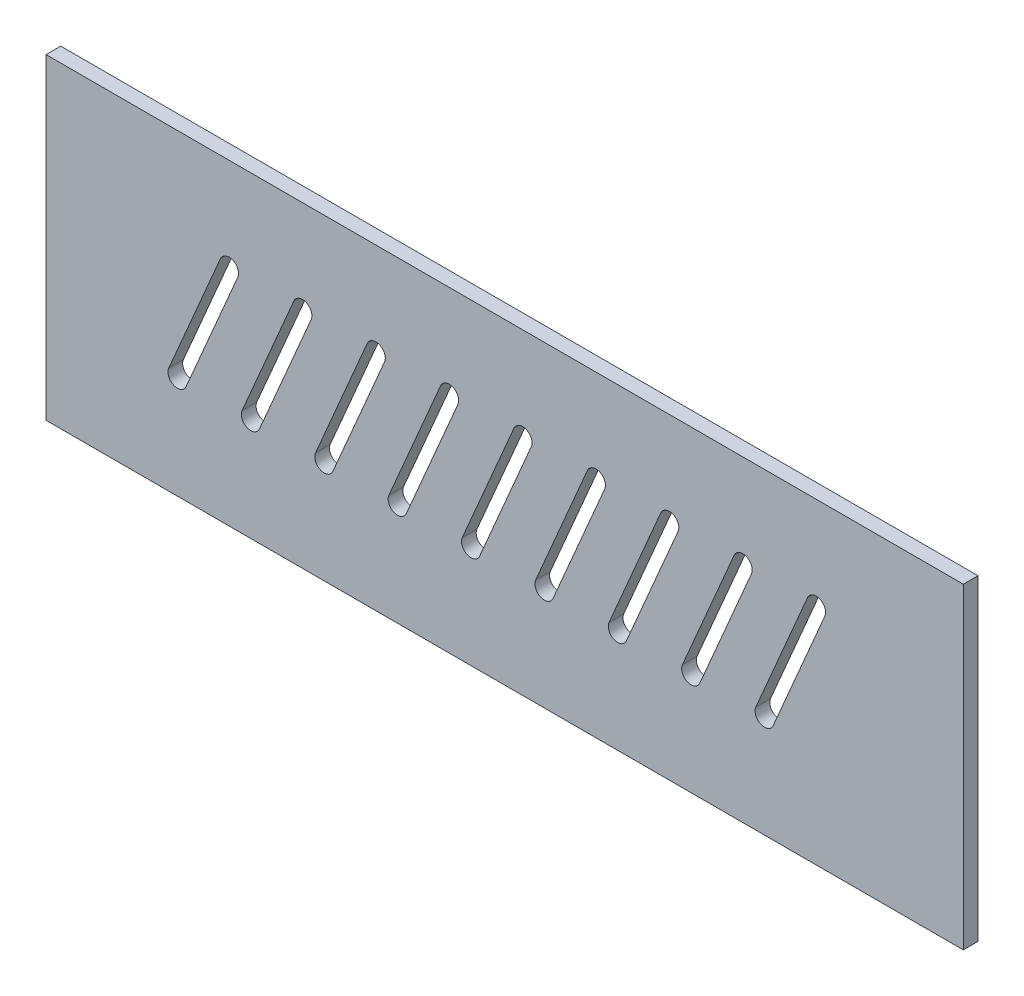
SolidWorks part; units mm, degrees
ref_plane "Front Plane" through (0, 0, 0) normal (0, 0, 1) x (1, 0, 0)
ref_plane "Top Plane" through (0, 0, 0) normal (0, 1, 0) x (1, 0, 0)
ref_plane "Right Plane" through (0, 0, 0) normal (1, 0, 0) x (0, 0, -1)
sketch "Sketch1" plane through (0, 0, 0) normal (0, 0, 1) x (1, 0, 0)
  line L1 (-62.5, 32.5) -> (62.5, 32.5)
  line L2 (-62.5, 32.5) -> (-62.5, -32.5)
  line L3 (-62.5, -32.5) -> (62.5, -32.5)
  line L4 (62.5, 32.5) -> (62.5, -32.5)
  line L5 (-62.5, 32.5) -> (62.5, -32.5) construction
  line L6 (-62.5, -32.5) -> (62.5, 32.5) construction
  point P0 (0, 0)
  dimension "D1" = 125
  dimension "D2" = 65
extrude "Boss-Extrude1" add sketch "Sketch1" along normal blind 2
sketch "Sketch2" plane through (0, 0, 2) normal (0, 0, 1) x (1, 0, 0)
  line L0 (62.5, -32.5) -> (62.5, 32.5) construction
  line L1 (-62.5, 32.5) -> (62.5, 32.5)
  line L2 (-62.5, 32.5) -> (-62.5, 10.6595)
  line L3 (-62.5, 10.6595) -> (62.5, 10.6595)
  line L4 (62.5, 32.5) -> (62.5, 10.6595)
extrude "Cut-Extrude1" cut sketch "Sketch2" against normal through all contours L3 L4 L1 L2
sketch "Sketch3" plane through (0, 0, 2) normal (0, 0, 1) x (1, 0, 0)
  line L0 (-44.5939, -18.483) -> (-37.5528, -2.0537) construction
  line L1 (-45.7742, -17.9772) -> (-38.733, -1.5478)
  line L2 (-43.4136, -18.9888) -> (-36.3725, -2.5595)
  arc A0 (-45.7742, -17.9772) -> (-43.4136, -18.9888) centre (-44.5939, -18.483) ccw
  arc A1 (-36.3725, -2.5595) -> (-38.733, -1.5478) centre (-37.5528, -2.0537) ccw
  point P2 (-41.0733, -10.2683)
extrude "Cut-Extrude2" cut sketch "Sketch3" against normal blind 20
pattern_linear "LPattern1" count 9 spacing 10 along (1, 0, 0) of "Cut-Extrude2"
